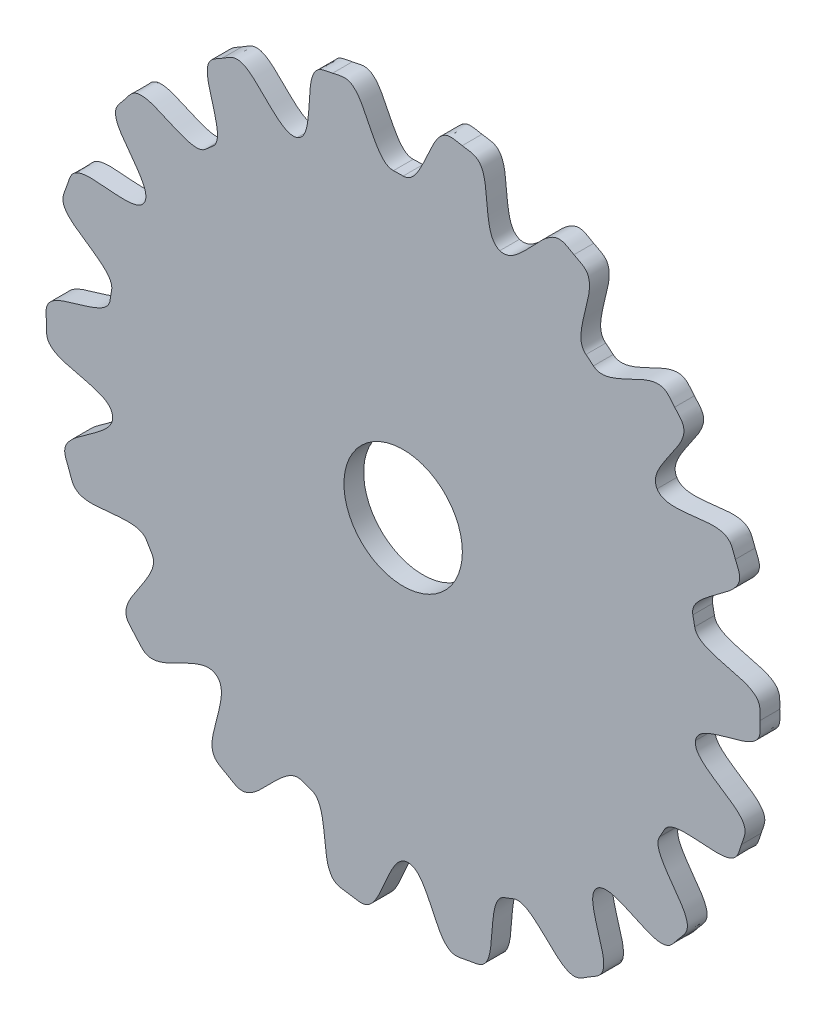
SolidWorks part; units mm, degrees
ref_plane "Front Plane" through (0, 0, 0) normal (0, 0, 1) x (1, 0, 0)
ref_plane "Top Plane" through (0, 0, 0) normal (0, 1, 0) x (1, 0, 0)
ref_plane "Right Plane" through (0, 0, 0) normal (1, 0, 0) x (0, 0, -1)
sketch "Sketch2" plane through (0, 0, 0) normal (0, 0, 1) x (1, 0, 0)
  circle A0 centre (0, 0) radius 15
  circle A1 centre (0, 0) radius 75.0001
  spline S0 degree 3 poles (0, 75.0001) (1.8947, 75.0001) (6.1889, 80.8404) (8.5648, 90.7366) (13.6354, 89.3867) (14.9723, 89.1622) knots 0 0 0 0 0.259469 0.853077 1 1 1 1
  spline S1 degree 3 poles (24.4975, 70.8864) (22.7068, 71.5052) (20.5558, 78.4278) (21.5426, 88.5574) (16.3092, 88.9377) (14.9723, 89.1622) knots 0 0 0 0 0.259469 0.853077 1 1 1 1
  spline S2 degree 3 poles (24.4975, 70.8864) (26.2883, 70.2675) (32.2546, 74.3849) (37.7327, 82.9623) (42.0842, 80.0302) (43.2745, 79.3813) knots 0 0 0 0 0.259469 0.853077 1 1 1 1
  spline S3 degree 3 poles (46.3078, 58.9966) (44.8174, 60.1665) (45.0455, 67.4119) (49.2868, 76.6636) (44.4647, 78.7324) (43.2745, 79.3813) knots 0 0 0 0 0.259469 0.853077 1 1 1 1
  spline S4 degree 3 poles (48.2091, 57.4534) (49.6605, 56.2355) (56.7041, 57.9492) (64.8854, 64.0029) (67.902, 59.7095) (68.7818, 58.6782) knots 0 0 0 0 0.259469 0.853077 1 1 1 1
  spline S5 degree 3 poles (64.3311, 38.5554) (63.3571, 40.1806) (66.1591, 46.8662) (73.4262, 53.9916) (69.6617, 57.6469) (68.7818, 58.6782) knots 0 0 0 0 0.259469 0.853077 1 1 1 1
  spline S6 degree 3 poles (64.3311, 38.5554) (65.3051, 36.9302) (72.5221, 36.2493) (82.232, 39.2987) (83.6808, 34.2555) (84.1755, 32.9933) knots 0 0 0 0 0.259469 0.853077 1 1 1 1
  spline S7 degree 3 poles (73.3961, 15.428) (73.0063, 17.2821) (77.8384, 22.6859) (87.0343, 27.0467) (84.6702, 31.7311) (84.1755, 32.9933) knots 0 0 0 0 0.259469 0.853077 1 1 1 1
  spline S8 degree 3 poles (73.8606, 13.0236) (74.1896, 11.1577) (80.6869, 7.9429) (90.8454, 7.3215) (90.3965, 2.0936) (90.4075, 0.738) knots 0 0 0 0 0.259469 0.853077 1 1 1 1
  spline S9 degree 3 poles (74.0634, -11.8161) (74.3619, -9.9451) (80.8058, -6.6246) (90.9528, -5.8375) (90.4186, -0.6176) (90.4075, 0.738) knots 0 0 0 0 0.259469 0.853077 1 1 1 1
  spline S10 degree 3 poles (74.0634, -11.8161) (73.7649, -13.6871) (78.8557, -18.8478) (88.2541, -22.7532) (86.1222, -27.5477) (85.6898, -28.8326) knots 0 0 0 0 0.259469 0.853077 1 1 1 1
  spline S11 degree 3 poles (66.1416, -35.3596) (67.0348, -33.6887) (74.2099, -32.6552) (84.0574, -35.2256) (85.2575, -30.1175) (85.6898, -28.8326) knots 0 0 0 0 0.259469 0.853077 1 1 1 1
  spline S12 degree 3 poles (64.952, -37.5) (64.0046, -39.1409) (66.9154, -45.7799) (74.2978, -52.7857) (70.5935, -56.5019) (69.7306, -57.5475) knots 0 0 0 0 0.259469 0.853077 1 1 1 1
  spline S13 degree 3 poles (49.1406, -56.6587) (50.572, -55.4173) (57.6426, -57.0158) (65.9216, -62.9351) (68.8677, -58.5931) (69.7306, -57.5475) knots 0 0 0 0 0.259469 0.853077 1 1 1 1
  spline S14 degree 3 poles (49.1406, -56.6587) (47.7093, -57.9001) (48.2919, -65.1257) (52.9811, -74.1586) (48.2661, -76.4611) (47.109, -77.1674) knots 0 0 0 0 0.259469 0.853077 1 1 1 1
  spline S15 degree 3 poles (27.9387, -69.602) (29.697, -68.8962) (35.8577, -72.7165) (41.7492, -81.0154) (45.9519, -77.8738) (47.109, -77.1674) knots 0 0 0 0 0.259469 0.853077 1 1 1 1
  spline S16 degree 3 poles (25.6515, -70.477) (23.8711, -71.125) (21.8334, -78.0818) (22.9855, -88.1939) (17.759, -88.6596) (16.4259, -88.9059) knots 0 0 0 0 0.259469 0.853077 1 1 1 1
  spline S17 degree 3 poles (1.2244, -74.9901) (3.1188, -74.9591) (7.5078, -80.7286) (10.045, -90.5847) (15.0928, -89.1522) (16.4259, -88.9059) knots 0 0 0 0 0.259469 0.853077 1 1 1 1
  spline S18 degree 3 poles (1.2244, -74.9901) (-0.67, -75.021) (-4.8683, -80.9306) (-7.0824, -90.8644) (-12.1743, -89.5974) (-13.5147, -89.3947) knots 0 0 0 0 0.259469 0.853077 1 1 1 1
  spline S19 degree 3 poles (-23.337, -71.2769) (-21.5364, -71.8664) (-19.2727, -78.753) (-20.094, -88.8973) (-14.8551, -89.1921) (-13.5147, -89.3947) knots 0 0 0 0 0.259469 0.853077 1 1 1 1
  spline S20 degree 3 poles (-25.6515, -70.477) (-27.432, -69.829) (-33.4647, -73.8484) (-39.0821, -82.3352) (-43.3851, -79.3325) (-44.5646, -78.6642) knots 0 0 0 0 0.259469 0.853077 1 1 1 1
  spline S21 degree 3 poles (-47.2647, -58.2327) (-45.7936, -59.4268) (-46.14, -66.6676) (-50.5318, -75.8487) (-45.7442, -77.996) (-44.5646, -78.6642) knots 0 0 0 0 0.259469 0.853077 1 1 1 1
  spline S22 degree 3 poles (-47.2647, -58.2327) (-48.7358, -57.0387) (-55.7505, -58.8672) (-63.8319, -65.0537) (-66.9181, -60.8101) (-67.8147, -59.7933) knots 0 0 0 0 0.259469 0.853077 1 1 1 1
  spline S23 degree 3 poles (-63.6931, -39.6005) (-62.6927, -41.2095) (-65.3852, -47.94) (-72.535, -55.1831) (-68.7113, -58.7764) (-67.8147, -59.7933) knots 0 0 0 0 0.259469 0.853077 1 1 1 1
  spline S24 degree 3 poles (-64.952, -37.5) (-65.8993, -35.8592) (-73.1042, -35.0605) (-82.8626, -37.951) (-84.2288, -32.8848) (-84.7029, -31.6147) knots 0 0 0 0 0.259469 0.853077 1 1 1 1
  spline S25 degree 3 poles (-73.6382, -14.2277) (-73.2787, -16.088) (-78.1984, -21.4121) (-87.4642, -25.6223) (-85.1769, -30.3446) (-84.7029, -31.6147) knots 0 0 0 0 0.259469 0.853077 1 1 1 1
  spline S26 degree 3 poles (-73.6382, -14.2277) (-73.9976, -12.3674) (-80.5465, -9.2591) (-90.7138, -8.8037) (-90.3502, -3.5691) (-90.3834, -2.2139) knots 0 0 0 0 0.259469 0.853077 1 1 1 1
  spline S27 degree 3 poles (-74.2464, 10.6054) (-74.5144, 8.7297) (-80.9032, 5.3046) (-91.036, 4.3519) (-90.4166, -0.8586) (-90.3834, -2.2139) knots 0 0 0 0 0.259469 0.853077 1 1 1 1
  spline S28 degree 3 poles (-73.8606, 13.0236) (-73.5316, 14.8895) (-78.5375, 20.1326) (-87.8709, 24.191) (-85.661, 28.95) (-85.2077, 30.2277) knots 0 0 0 0 0.259469 0.853077 1 1 1 1
  spline S29 degree 3 poles (-65.5555, 36.4347) (-66.4759, 34.7786) (-73.6669, 33.8623) (-83.4712, 36.5931) (-84.7545, 31.5053) (-85.2077, 30.2277) knots 0 0 0 0 0.259469 0.853077 1 1 1 1
  spline S30 degree 3 poles (-65.5555, 36.4347) (-64.6351, 38.0908) (-67.6538, 44.6814) (-75.1497, 51.5657) (-71.5065, 55.3419) (-70.6608, 56.4014) knots 0 0 0 0 0.259469 0.853077 1 1 1 1
  spline S31 degree 3 poles (-50.0591, 55.8489) (-51.4699, 54.5843) (-58.5657, 56.0671) (-66.9403, 61.8505) (-69.8151, 57.461) (-70.6608, 56.4014) knots 0 0 0 0 0.259469 0.853077 1 1 1 1
  spline S32 degree 3 poles (-48.2091, 57.4534) (-46.7577, 58.6713) (-47.2222, 65.9054) (-51.7633, 75.0137) (-47.0114, 77.2388) (-45.8429, 77.9262) knots 0 0 0 0 0.259469 0.853077 1 1 1 1
  spline S33 degree 3 poles (-26.7987, 70.0488) (-28.5683, 69.3718) (-34.6658, 73.2922) (-40.421, 81.6862) (-44.6745, 78.6136) (-45.8429, 77.9262) knots 0 0 0 0 0.259469 0.853077 1 1 1 1
  spline S34 degree 3 poles (-26.7987, 70.0488) (-25.0291, 70.7258) (-23.1052, 77.715) (-24.4222, 87.8069) (-19.204, 88.3579) (-17.8751, 88.6259) knots 0 0 0 0 0.259469 0.853077 1 1 1 1
  spline S35 degree 3 poles (-2.4485, 74.9601) (-4.3422, 74.8982) (-8.8247, 80.5952) (-11.5225, 90.4087) (-16.5462, 88.8939) (-17.8751, 88.6259) knots 0 0 0 0 0.259469 0.853077 1 1 1 1
  point P124 (0, 0)
extrude "Boss-Extrude2" add sketch "Sketch2" along normal blind 5 contours A1 S3 S2 | A1 S5 S4 | A1 S7 S6 | A1 S9 S8 | A1 S11 S10 | A1 S13 S12 | A1 S15 S14 | A1 S17 S16 | A1 S19 S18 | A1 S21 S20 | A1 S23 S22 | A1 S25 S24 | A1 S27 S26 | A1 S29 S28 | A1 S31 S30 | A1 S33 S32 | A1 S35 S34 | A1 S1 S0 | A1 A0
